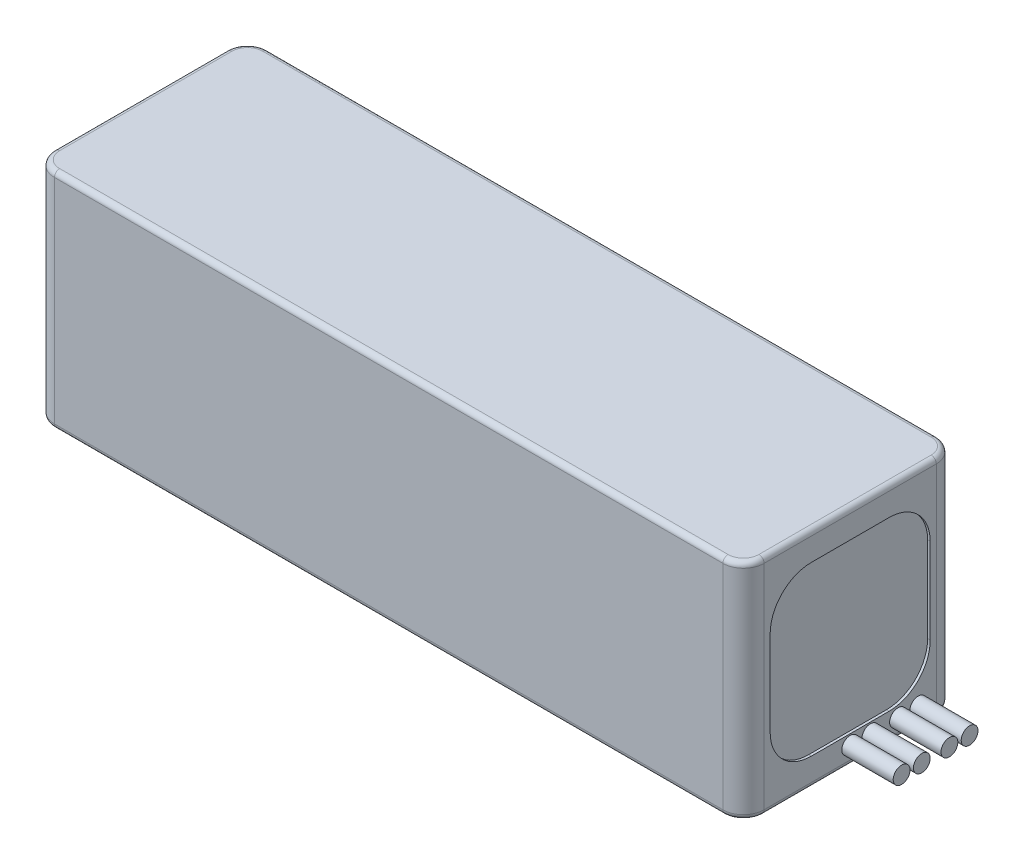
SolidWorks part; units mm, degrees
ref_plane "Front Plane" through (0, 0, 0) normal (0, 0, 1) x (1, 0, 0)
ref_plane "Top Plane" through (0, 0, 0) normal (0, 1, 0) x (1, 0, 0)
ref_plane "Right Plane" through (0, 0, 0) normal (1, 0, 0) x (0, 0, -1)
ref_plane "Plane1" through (0, 0, -15) normal (0, 0, -1) x (-1, 0, 0)
sketch "Sketch1" plane through (0, 0, -15) normal (0, 0, -1) x (-1, 0, 0)
  line L0 (-69, -22) -> (69, -22)
  line L1 (69, -22) -> (69, 21.5)
  line L2 (69, 21.5) -> (-69, 21.5)
  line L3 (-69, 21.5) -> (-69, -22)
  line L4 (-69, -0.25) -> (69, -0.25) construction
  line L5 (0, 21.5) -> (0, -22) construction
  dimension "D1" = 43.5
  dimension "D2" = 138
extrude "Boss-Extrude1" add sketch "Sketch1" against normal blind 41.5
sketch "Sketch2" plane through (69, 0, 0) normal (1, 0, 0) x (0, 0, -1)
  line L0 (-21.3125, 8.0625) -> (-21.3125, -8.5625)
  line L1 (-13.3125, -16.5625) -> (1.8125, -16.5625)
  line L2 (9.8125, -8.5625) -> (9.8125, 8.0625)
  line L3 (1.8125, 16.0625) -> (-13.3125, 16.0625)
  line L4 (-26.5, 21.5) -> (15, -22) construction
  line L5 (15, 21.5) -> (-26.5, -22) construction
  line L6 (-21.3125, 16.0625) -> (9.8125, -16.5625) construction
  line L7 (9.8125, 16.0625) -> (-21.3125, -16.5625) construction
  line L12 (-26.5, 21.5) -> (15, 21.5) construction
  line L13 (-26.5, 21.5) -> (-26.5, -22) construction
  line L14 (-26.5, -22) -> (15, -22) construction
  line L15 (15, 21.5) -> (15, -22) construction
  line L16 (-26.5, 21.5) -> (15, -22) construction
  line L17 (-26.5, -22) -> (15, 21.5) construction
  arc A0 (-21.3125, -8.5625) -> (-13.3125, -16.5625) centre (-13.3125, -8.5625) ccw
  arc A1 (1.8125, -16.5625) -> (9.8125, -8.5625) centre (1.8125, -8.5625) ccw
  arc A2 (9.8125, 8.0625) -> (1.8125, 16.0625) centre (1.8125, 8.0625) ccw
  arc A3 (-21.3125, 8.0625) -> (-13.3125, 16.0625) centre (-13.3125, 8.0625) cw
  point P16 (-5.75, -0.25)
  dimension "D3" = 8
  dimension "D1" = 31.125
  dimension "D2" = 41.5
extrude "Cut-Extrude1" cut sketch "Sketch2" against normal blind 0.5
sketch "Sketch3" plane through (-69, 0, 0) normal (-1, 0, 0) x (0, 0, 1)
  line L0 (13.3125, 16.0625) -> (-1.8125, 16.0625)
  line L1 (-9.8125, 8.0625) -> (-9.8125, -8.5625)
  line L2 (-1.8125, -16.5625) -> (13.3125, -16.5625)
  line L3 (21.3125, -8.5625) -> (21.3125, 8.0625)
  line L4 (-9.8125, 16.0625) -> (21.3125, -16.5625) construction
  line L5 (21.3125, 16.0625) -> (-9.8125, -16.5625) construction
  line L6 (-15, 21.5) -> (26.5, -22) construction
  line L7 (26.5, -22) -> (-15, -22) construction
  line L8 (-15, -22) -> (26.5, 21.5) construction
  arc A0 (-9.8125, -8.5625) -> (-1.8125, -16.5625) centre (-1.8125, -8.5625) ccw
  arc A1 (13.3125, -16.5625) -> (21.3125, -8.5625) centre (13.3125, -8.5625) ccw
  arc A2 (13.3125, 16.0625) -> (21.3125, 8.0625) centre (13.3125, 8.0625) cw
  arc A3 (-1.8125, 16.0625) -> (-9.8125, 8.0625) centre (-1.8125, 8.0625) ccw
  dimension "D3" = 8
  dimension "D1" = 31.125
  dimension "D2" = 41.5
extrude "Cut-Extrude2" cut sketch "Sketch3" against normal blind 0.5
fillet "Fillet1" radius 4 4 edges at (-69, -0.25, -15) (-69, -0.25, 26.5) (69, -0.25, -15) (69, -0.25, 26.5)
fillet "Fillet2" radius 1 16 edges at (67.8284, 21.5, -13.8284) (69, 21.5, 5.75) (0, 21.5, -15) (67.8284, 21.5, 25.3284) (-67.8284, 21.5, -13.8284) (0, 21.5, 26.5) (-69, 21.5, 5.75) (-67.8284, 21.5, 25.3284) (-69, -22, 5.75) (-67.8284, -22, -13.8284) (-67.8284, -22, 25.3284) (0, -22, -15) (0, -22, 26.5) (67.8284, -22, -13.8284) (67.8284, -22, 25.3284) (69, -22, 5.75)
sketch "Sketch4" plane through (0, 0, 26.5) normal (0, 0, 1) x (1, 0, 0)
  line L0 (-65, -0.25) -> (65, -0.25) construction
  line L1 (-65, 20.5) -> (-65, -21) construction
  line L2 (65, -21) -> (65, 20.5) construction
  line L3 (0, 25.9735) -> (0, -21) construction
  line L4 (-65, -21) -> (65, -21) construction
  circle A0 centre (0, -0.25) radius 0.5026
sketch "Sketch5" plane through (69, 0, 0) normal (-1, 0, 0) x (0, 0, 1)
  circle A0 centre (-7.4743, -18.4804) radius 1.635
  circle A1 centre (-3.5518, -18.4804) radius 1.635
  circle A2 centre (1.8218, -18.4804) radius 1.635
  circle A3 centre (5.75, -18.4804) radius 1.635
  point P4 (-7.4743, -18.3282)
  point P5 (-3.5518, -18.2915)
  point P8 (0.8126, -18.2915)
  point P11 (5.75, -19.2411)
  point P12 (0, 0)
  point P13 (1.8218, -18.4804)
  dimension "D1" = 3.27
  dimension "D2" = 3.27
  dimension "D3" = 3.27
  dimension "D4" = 3.27
extrude "Boss-Extrude2" add sketch "Sketch5" against normal blind 10
equation "\"D1@Sketch3\"=\"D2@Sketch3\" * .75"
equation "\"D1@Sketch2\"=\"D2@Sketch2\"* .75"
